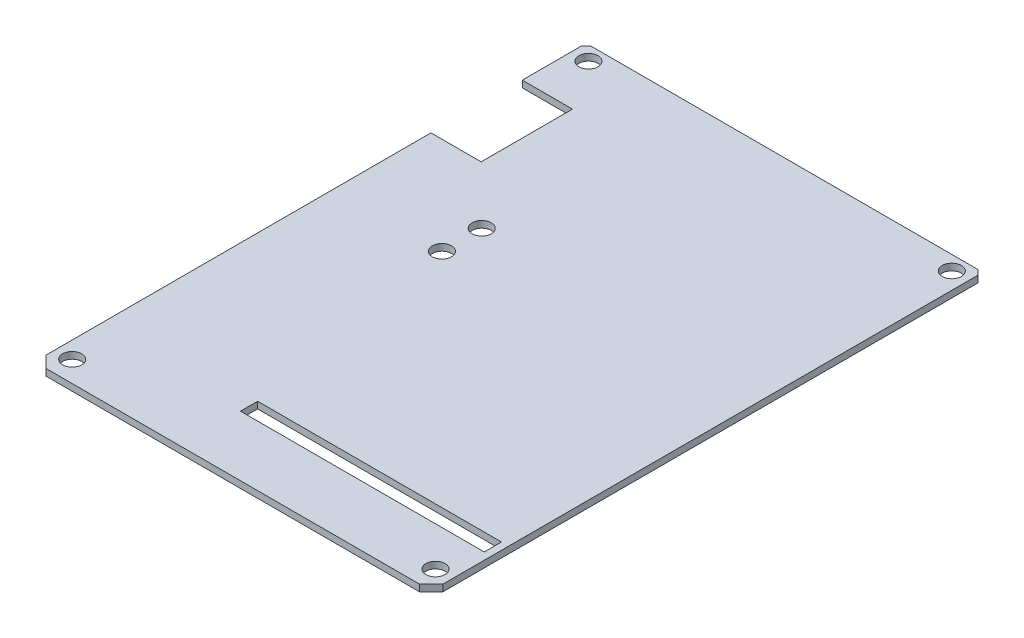
SolidWorks part; units mm, degrees
ref_plane "Front Plane" through (0, 0, 0) normal (0, 0, 1) x (1, 0, 0)
ref_plane "Top Plane" through (0, 0, 0) normal (0, 1, 0) x (1, 0, 0)
ref_plane "Right Plane" through (0, 0, 0) normal (1, 0, 0) x (0, 0, -1)
sketch "Sketch1" plane through (0, 0, 0) normal (0, 1, 0) x (1, 0, 0)
  line L17 (21.25, -27.4901) -> (19.2401, -29.5)
  line L33 (-21.25, 29.5) -> (21.25, 29.5)
  line L34 (-21.25, 29.5) -> (-21.25, -29.5)
  line L35 (-21.25, -29.5) -> (21.25, -29.5)
  line L36 (21.25, 29.5) -> (21.25, -29.5)
  line L37 (-21.25, 29.5) -> (21.25, -29.5) construction
  line L38 (-21.25, -29.5) -> (21.25, 29.5) construction
  line L39 (0, -29.5) -> (0, 29.5) construction
  line L40 (-21.25, -27.4901) -> (-19.2401, -29.5)
  line L41 (21.25, 0) -> (-21.25, 0) construction
  line L42 (21.25, 27.4901) -> (19.2401, 29.5)
  line L43 (-21.25, 27.4901) -> (-19.2401, 29.5)
  line L44 (-20.2401, 28.5) -> (20.2401, 28.5)
  line L45 (-20.2401, -28.5) -> (20.2401, -28.5)
  line L46 (-20.75, -27.9901) -> (-20.75, 27.9901)
  line L47 (20.75, 27.9901) -> (20.75, -27.9901)
  line L56 (-19, -27) -> (19, -27) construction
  circle A13 centre (-9.45, 6.2845) radius 1
  circle A18 centre (-19, -27) radius 1
  circle A19 centre (19, -27) radius 1
  circle A22 centre (-19, 27) radius 1
  circle A23 centre (19, 27) radius 1
  circle A24 centre (-9.45, 2.1155) radius 1
  point P4 (0, 0)
  point P14 (0, 0)
  point P21 (0, -27)
  point P24 (-12.6269, 17.0486)
  dimension "D1" = 42.5
  dimension "D6" = 2.0099
  dimension "D9" = 2
  dimension "D3" = 19
  dimension "D5" = 2.0099
  dimension "D2" = 59
  dimension "D12" = 1
  dimension "D4" = 2
  dimension "D8" = 27
  dimension "D13" = 0.5
  dimension "D14" = 0.5
extrude "Boss-Extrude1" add sketch "Sketch1" along normal blind 0.7
sketch "Sketch2" plane through (0, 0.7, 0) normal (0, 1, 0) x (1, 0, 0)
  line L1 (-20, -22.9) -> (20, -22.9)
  line L2 (-20, -22.9) -> (-20, -21.1)
  line L3 (-20, -21.1) -> (20, -21.1)
  line L4 (20, -22.9) -> (20, -21.1)
  line L5 (-20, -22.9) -> (20, -21.1) construction
  line L6 (-20, -21.1) -> (20, -22.9) construction
  line L7 (0, 0) -> (0, -22.9) construction
  line L10 (-5.5029, -21.1) -> (-5.5029, -22.9)
  line L11 (-5.25, -22.6) -> (-5.25, -21.1) construction
  point P4 (0, -22)
  dimension "D1" = 22
  dimension "D2" = 20
  dimension "D3" = 1.8
  dimension "D4" = 0.2529
extrude "Cut-Extrude1" cut sketch "Sketch2" against normal blind 10 contours L3 L10 L1 L4
sketch "Sketch5" plane through (0, 0.7, 0) normal (0, 1, 0) x (1, 0, 0)
  line L0 (-20.2401, -28.5) -> (20.2401, -28.5) construction
  line L1 (-19.5401, -28.5) -> (19.5401, -28.5) construction
  line L2 (-19.5401, -28.5) -> (-19.5401, -29.2) construction
  line L3 (-19.5401, -29.2) -> (19.5401, -29.2)
  line L4 (19.5401, -28.5) -> (19.5401, -29.2) construction
  line L5 (-19.5401, -28.5) -> (19.5401, -29.2) construction
  line L6 (-19.5401, -29.2) -> (19.5401, -28.5) construction
  line L7 (0, -28.5) -> (0, -32.1934) construction
  line L9 (-19.5401, -29.2) -> (-20.2401, -28.5)
  line L10 (19.5401, -29.2) -> (20.2401, -28.5)
  line L11 (-20.2401, -28.5) -> (20.2401, -28.5)
  line L12 (-20.75, -27.9901) -> (-20.2401, -28.5) construction
  point P4 (0, -28.85)
  dimension "D1" = 0.7
extrude "Boss-Extrude2" add sketch "Sketch5" against normal up to surface (0.7 mm away) up to face at (19, 0, -26)
sketch "Sketch6" plane through (0, 0.7, 0) normal (0, 1, 0) x (1, 0, 0)
  line L0 (-20.75, -27.9901) -> (-20.75, 27.9901) construction
  line L1 (-20.75, 21.8236) -> (-15.5, 21.8236)
  line L2 (-20.75, 21.8236) -> (-20.75, 12.2736)
  line L3 (-20.75, 12.2736) -> (-15.5, 12.2736)
  line L4 (-15.5, 21.8236) -> (-15.5, 12.2736)
  line L5 (-20.75, 21.8236) -> (-15.5, 12.2736) construction
  line L6 (-20.75, 12.2736) -> (-15.5, 21.8236) construction
  line L7 (-12.75, 17.0486) -> (-25.5525, 17.0486) construction
  line L8 (-12.75, 21.4236) -> (-12.75, 12.6736) construction
  point P4 (-18.125, 17.0486)
  dimension "D1" = 9.55
  dimension "D2" = 5.25
extrude "Cut-Extrude2" cut sketch "Sketch6" against normal blind 6
